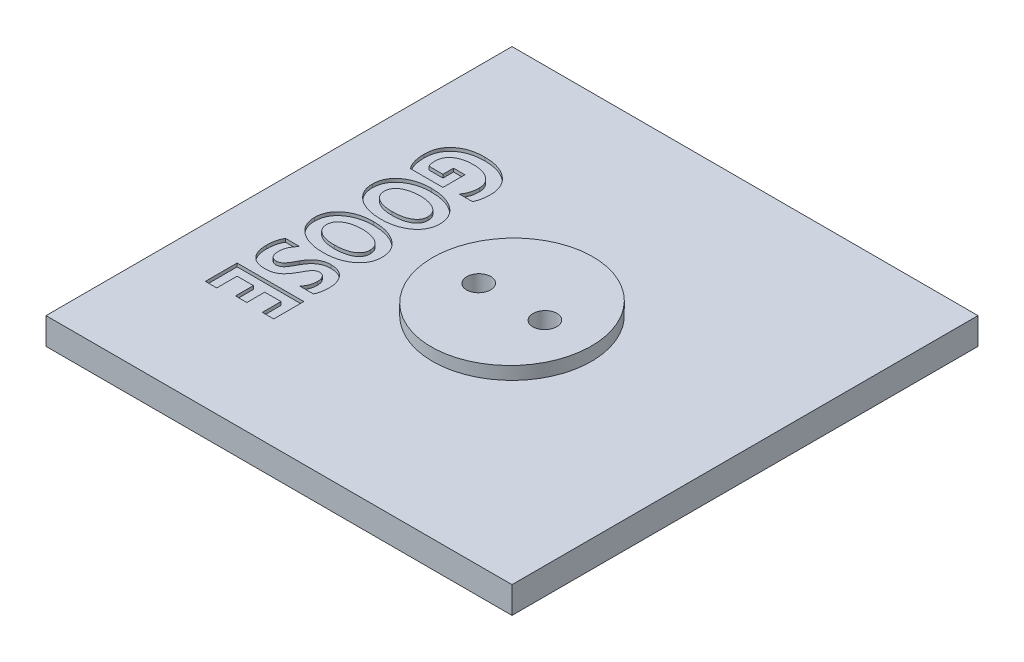
SolidWorks part; units mm, degrees
ref_plane "Front Plane" through (0, 0, 0) normal (0, 0, 1) x (1, 0, 0)
ref_plane "Top Plane" through (0, 0, 0) normal (0, 1, 0) x (1, 0, 0)
ref_plane "Right Plane" through (0, 0, 0) normal (1, 0, 0) x (0, 0, -1)
sketch "Sketch1" plane through (0, 0, 0) normal (0, 1, 0) x (1, 0, 0)
  line L1 (0, 0) -> (69.85, 0)
  line L2 (0, 0) -> (0, 69.85)
  line L3 (0, 69.85) -> (69.85, 69.85)
  line L4 (69.85, 0) -> (69.85, 69.85)
  dimension "D1" = 69.85
extrude "Boss-Extrude1" add sketch "Sketch1" along normal blind 4
sketch "Sketch2" plane through (0, 4, 0) normal (0, 1, 0) x (1, 0, 0)
  line L0 (0, 0) -> (69.85, 0) construction
  line L9 (0, 0) -> (34.925, 0) construction
  line L14 (0, 0) -> (0, 34.925) construction
  line L15 (0, 34.925) -> (34.925, 34.925) construction
  line L16 (34.925, 0) -> (34.925, 34.925) construction
  circle A0 centre (34.925, 34.925) radius 11.9062
  point P7 (34.925, 0)
  dimension "D1" = 23.8125
extrude "Boss-Extrude2" add sketch "Sketch2" along direction (0, -1, 0) on the side of the normal blind 2
sketch "Sketch4" plane through (0, 0, 0) normal (0, 0, -1) x (-1, 0, 0)
  line L3 (-46.8312, 6) -> (-24.9423, 6) construction
  line L4 (-23.0187, 6) -> (-46.8312, 6) construction
  line L5 (-46.8312, 6) -> (-23.0187, 6)
  line L6 (-23.0187, 6) -> (-23.0187, 5.5844)
  line L7 (-26.2709, 5.6411) -> (-45.4903, 5.9766) construction
  line L8 (-46.8312, 6) -> (-23.0187, 5.5844)
  point P2 (-23.0187, 6)
  point P3 (-46.8312, 6)
  point P12 (-23.0187, 8.0314)
  point P13 (-23.0187, 7.5983)
  point P14 (-46.8312, 6)
  point P16 (-23.0187, 4.451)
  point P17 (-23.0187, 6)
  dimension "D1" = 1
extrude "Cut-Extrude2" cut sketch "Sketch4" along normal through all
sketch "Sketch5" plane through (-0.0904, 5.181, 0) normal (-0.0175, 0.9998, 0) x (0.9998, 0.0175, 0)
  line L0 (23.1127, 34.925) -> (46.9288, 34.925) construction
  ellipse E0 centre (35.0208, 34.925) end of major axis (23.1127, 34.925) minor radius 11.9062 construction
  point P8 (23.1127, 34.925)
sketch "Sketch3" plane through (0.0071, 5.1827, 0) normal (-0.0175, 0.9998, 0) x (0.9998, 0.0175, 0)
  line L0 (-0.0278, 34.925) -> (69.8116, 34.925) construction
  line L1 (-0.0278, 69.85) -> (-0.0278, 0) construction
  line L2 (69.8116, 0) -> (69.8116, 69.85) construction
  line L3 (31.7169, 34.925) -> (38.0669, 34.925) construction
  line L4 (28.145, 34.925) -> (41.6388, 34.925) construction
  line L5 (28.145, 34.925) -> (28.145, 44.7143) construction
  line L6 (41.6388, 34.925) -> (41.6388, 44.7143) construction
  line L7 (28.145, 44.7143) -> (41.6388, 44.7143) construction
  line L8 (31.7169, 34.925) -> (31.7169, 44.7143) construction
  line L9 (38.0669, 34.925) -> (38.0669, 44.7143) construction
  line L10 (31.7169, 44.7143) -> (38.0669, 44.7143) construction
  circle A0 centre (29.931, 34.925) radius 1.7859
  circle A1 centre (39.8528, 34.925) radius 1.7859
  ellipse E0 centre (34.9232, 34.925) end of major axis (23.0151, 34.925) minor radius 11.9062 construction
  point P10 (34.8919, 44.7143)
  point P12 (29.931, 34.925)
  point P18 (28.145, 43.4301)
  point P22 (34.8919, 34.925)
  dimension "D1" = 6.35
  dimension "D2" = 13.4937
extrude "Cut-Extrude1" cut sketch "Sketch3" against normal up to surface (5.6747 mm away)
sketch "Sketch6" plane through (0, 4, 0) normal (0, 1, 0) x (1, 0, 0)
  line L0 (7.5, 69.85) -> (7.5, 0) construction
  line L1 (69.85, 69.85) -> (0, 69.85) construction
  line L2 (0, 0) -> (69.85, 0) construction
  line L3 (17.5, 69.85) -> (17.5, 0) construction
  line L4 (7.5, 69.85) -> (17.5, 69.85) construction
  line L5 (23.0187, 34.925) -> (0, 34.925) construction
  line L6 (0, 69.85) -> (0, 0) construction
  circle A0 centre (34.925, 34.925) radius 11.9062 construction
  text T0 "<b>GOOSE</b>" font "@Microsoft YaHei" height 10
  point P15 (12.5, 69.85)
  dimension "D1" = 10
  dimension "D2" = 12.5
extrude "Cut-Extrude3" cut sketch "Sketch6" against normal blind 0.5
equation "\".0q\"=0"
